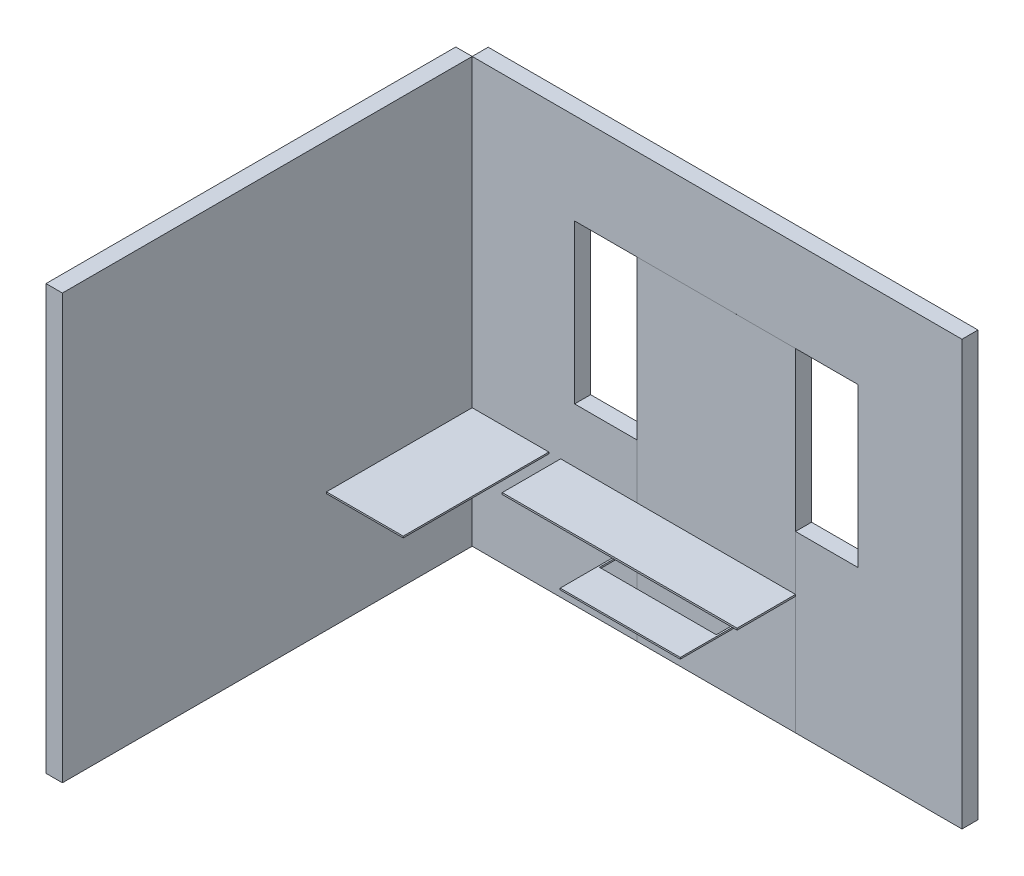
SolidWorks part; units mm, degrees
ref_plane "Plano frontal" through (0, 0, 0) normal (0, 0, 1) x (1, 0, 0)
ref_plane "Plano superior" through (0, 0, 0) normal (0, 1, 0) x (1, 0, 0)
ref_plane "Plano direito" through (0, 0, 0) normal (1, 0, 0) x (0, 0, -1)
sketch "Esboço6" plane through (0, 0, 0) normal (0, 0, 1) x (1, 0, 0)
  line L1 (0, 0) -> (3060, 0)
  line L2 (0, 0) -> (0, 2650)
  line L3 (0, 2650) -> (3060, 2650)
  line L4 (3060, 0) -> (3060, 2650)
extrude "Ressalto-extrusão2" add sketch "Esboço6" along normal blind 100
sketch "Esboço7" plane through (0, 0, 100) normal (0, 0, 1) x (1, 0, 0)
  line L2 (2020, 2080) -> (2020, 1090)
  line L3 (640, 2080) -> (640, 1090)
  line L4 (640, 2080) -> (1030, 2080)
  line L5 (1030, 2080) -> (1030, 1090)
  line L6 (1030, 1090) -> (640, 1090)
  line L7 (2020, 1090) -> (2410, 1090)
  line L8 (2410, 1090) -> (2410, 2080)
  line L9 (2410, 2080) -> (2020, 2080)
extrude "Corte-extrusão1" cut sketch "Esboço7" against normal blind 749
sketch "Esboço8" plane through (0, 0, 100) normal (0, 0, 1) x (1, 0, 0)
  line L0 (0, 2650) -> (-102.4312, 2650)
  line L1 (-102.4312, 2650) -> (-102.4312, 0)
  line L2 (-102.4312, 0) -> (0, 0)
  line L3 (0, 0) -> (0, 2650)
extrude "Ressalto-extrusão3" add sketch "Esboço8" along normal blind 2560 separate body
sketch "Esboço9" plane through (0, 0, 100) normal (0, 0, 1) x (1, 0, 0)
  line L1 (0, 0) -> (0, 2650) construction
  line L2 (0, 739.3899) -> (479.152, 739.3899)
  line L3 (479.152, 739.3899) -> (479.152, 749.3899)
  line L4 (479.152, 749.3899) -> (0, 749.3899)
  line L5 (0, 749.3899) -> (0, 739.3899)
extrude "Ressalto-extrusão5" add sketch "Esboço9" along normal blind 910 separate body
sketch "Esboço12" plane through (0, 0, 100) normal (0, 0, 1) x (1, 0, 0)
  line L1 (552.8669, 749.3899) -> (2020, 749.3899)
  line L2 (2020, 749.3899) -> (2020, 738.5475)
  line L3 (552.8669, 738.7437) -> (552.8669, 749.3899)
  line L4 (2020, 738.5475) -> (552.8669, 738.7437)
extrude "Ressalto-extrusão7" add sketch "Esboço12" along normal blind 365
sketch "Esboço13" plane through (0, 0, 100) normal (0, 0, 1) x (1, 0, 0)
  line L0 (1030, 2080) -> (2020, 2080)
  line L1 (2020, 2080) -> (2020, 749.3899)
  line L2 (2020, 749.3899) -> (552.8669, 749.3899) construction
  line L3 (1030, 2080) -> (1030, 749.3899)
  line L4 (1030, 749.3899) -> (2020, 749.3899)
  line L5 (2020, 738.5475) -> (2020, 0)
  line L6 (0, 0) -> (3060, 0) construction
  line L7 (2020, 0) -> (1030, 0)
  line L8 (1030, 0) -> (1030, 738.6799)
  line L9 (552.8669, 738.7437) -> (2020, 738.5475) construction
  line L10 (1030, 738.6799) -> (2020, 738.5475)
  point P14 (0, 0)
  point P19 (0, 0)
extrude "Ressalto-extrusão8" add sketch "Esboço13" along normal blind 0.01
sketch "Esboço14" plane through (0, 0, 100.01) normal (0, 0, 1) x (1, 0, 0)
  line L0 (1150, 648.6137) -> (1900, 648.6137)
  line L4 (1900, 648.6137) -> (1900, 638.6137)
  line L5 (1900, 638.6137) -> (1150, 638.6137)
  line L6 (1150, 638.6137) -> (1150, 648.6137)
extrude "Ressalto-extrusão9" add sketch "Esboço14" along normal blind 600
sketch "Esboço16" plane through (0, 638.6137, 0) normal (0, -1, 0) x (1, 0, 0)
  line L0 (1160, 100.01) -> (1890, 100.01)
  line L4 (1150, 100.01) -> (1900, 100.01) construction
  line L5 (1160, 100.01) -> (1160, 465.01)
  line L6 (1030, 100.01) -> (2020, 100.01) construction
  line L7 (1890, 100.01) -> (1890, 465.01)
  line L8 (1890, 465.01) -> (1160, 465.01)
extrude "Corte-extrusão2" cut sketch "Esboço16" against normal blind 45
